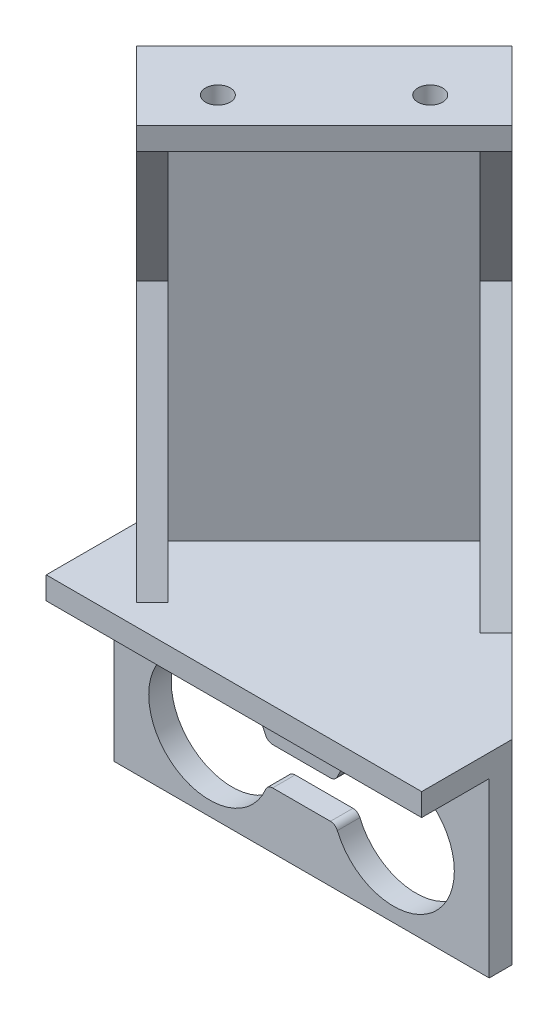
SolidWorks part; units mm, degrees
other "标注1"
sketch "草图6" plane through (25, -10, 15) normal (0.0929, -0.9273, 0.3626) x (0.5024, 0.3581, 0.787)
other "标注2"
sketch "草图7" plane through (25, -10, 15) normal (0.0929, -0.9273, 0.3626) x (0.5024, 0.3581, 0.787)
other "标注3"
sketch "草图8" plane through (25, -10, 15) normal (0.0929, -0.9273, 0.3626) x (0.5024, 0.3581, 0.787)
ref_plane "前视基准面" through (0, 0, 0) normal (0, 0, 1) x (1, 0, 0)
ref_plane "上视基准面" through (0, 0, 0) normal (0, 1, 0) x (1, 0, 0)
ref_plane "右视基准面" through (0, 0, 0) normal (1, 0, 0) x (0, 0, -1)
sketch "草图1" plane through (0, 0, 0) normal (0, 0, 1) x (1, 0, 0)
  line L1 (25, -10) -> (-25, -10)
  line L2 (25, -10) -> (25, 10)
  line L3 (25, 10) -> (-25, 10)
  line L4 (-25, -10) -> (-25, 10)
  line L5 (25, -10) -> (-25, 10) construction
  line L6 (25, 10) -> (-25, -10) construction
  line L8 (-3.85, 2.5) -> (3.85, 2.5)
  line L9 (3.85, -2.5) -> (-3.85, -2.5)
  line L10 (3.25, 7.25) -> (-3.25, 7.25) construction
  line L11 (3.25, 5.5) -> (-3.25, 5.5)
  line L12 (3.25, 9) -> (-3.25, 9)
  arc A7 (4.7731, -3.1154) -> (4.7731, 3.1154) centre (12.25, 0) ccw
  arc A8 (-4.7731, 3.1154) -> (-4.7731, -3.1154) centre (-12.25, 0) ccw
  arc A9 (3.85, -2.5) -> (4.7731, -3.1154) centre (3.85, -3.5) cw
  arc A10 (3.85, 2.5) -> (4.7731, 3.1154) centre (3.85, 3.5) ccw
  arc A11 (-3.85, -2.5) -> (-4.7731, -3.1154) centre (-3.85, -3.5) ccw
  arc A12 (-3.85, 2.5) -> (-4.7731, 3.1154) centre (-3.85, 3.5) cw
  arc A13 (3.25, 5.5) -> (3.25, 9) centre (3.25, 7.25) ccw
  arc A14 (-3.25, 9) -> (-3.25, 5.5) centre (-3.25, 7.25) ccw
  point P0 (0, 0)
  point P22 (0, 7.25)
  dimension "D3" = 1
  dimension "D4" = 8.1
  dimension "D5" = 8.1
  dimension "D6" = 2.5
  dimension "D8" = 12.25
  dimension "D9" = 12.25
  dimension "D12" = 1.75
  dimension "D1" = 20
  dimension "D2" = 50
  dimension "D7" = 2.5
  dimension "D10" = 7.25
  dimension "D11" = 6.5
  dimension "D13" = 3.25
extrude "凸台-拉伸1" add sketch "草图1" along normal blind 3
sketch "草图2" plane through (0, 10, 0) normal (0, 1, 0) x (1, 0, 0)
  line L1 (-25, 0) -> (25, 0)
  line L2 (-25, 0) -> (-25, -12)
  line L3 (-25, -12) -> (25, -12)
  line L4 (25, 0) -> (25, -12)
  dimension "D1" = 12
extrude "凸台-拉伸2" add sketch "草图2" along normal blind 6
sketch "草图5" plane through (0, 10, 0) normal (0, -1, 0) x (1, 0, 0)
  line L1 (25, 3) -> (-25, 3)
  line L2 (25, 3) -> (25, 12)
  line L3 (25, 12) -> (-25, 12)
  line L4 (-25, 3) -> (-25, 12)
extrude "切除-拉伸2" cut sketch "草图5" against normal blind 3
sketch "草图9" plane through (0, 16, 0) normal (0, 1, 0) x (1, 0, 0)
  line L0 (25, 0) -> (0, 25)
  line L1 (0, 25) -> (-25, 0)
  line L2 (25, 0) -> (-25, 0)
extrude "凸台-拉伸3" add sketch "草图9" against normal blind 3
sketch "草图11" plane through (0, 16, 0) normal (0, 1, 0) x (1, 0, 0)
  line L0 (0, 25) -> (2.1213, 22.8787)
  line L1 (25, 0) -> (0, 25) construction
  line L2 (2.1213, 22.8787) -> (-22.8787, -2.1213)
  line L3 (-25, 0) -> (-22.8787, -2.1213)
  line L9 (-25, 0) -> (-25, -12)
  line L10 (-25, -12) -> (25, -12)
  line L11 (25, -12) -> (25, 0)
  line L12 (25, 0) -> (0, 25)
  line L13 (0, 25) -> (-25, 0)
  line L18 (0, 25) -> (-25, 0)
  dimension "D1" = 0
extrude "凸台-拉伸4" add sketch "草图11" along normal blind 55 contours L18 L3 L2 L0
sketch "草图12" plane through (-10.3787, 0, -10.3787) normal (0.7071, 0, 0.7071) x (0.7071, 0, -0.7071)
  line L2 (-17.6777, 71) -> (-17.6777, 68)
  line L5 (14.6777, 68) -> (-17.6777, 68)
  line L6 (14.6777, 68) -> (14.6777, 71)
  line L7 (14.6777, 71) -> (-17.6777, 71)
extrude "凸台-拉伸6" add sketch "草图12" along normal blind 10
sketch "草图13" plane through (12.5, 0, -12.5) normal (0.7071, 0, -0.7071) x (-0.7071, 0, -0.7071)
  line L0 (17.6777, 71) -> (4.6777, 71)
  line L1 (17.6777, 71) -> (17.6777, 46)
  line L2 (17.6777, 13) -> (17.6777, 71) construction
  line L3 (4.6777, 71) -> (4.6777, 68)
  line L4 (17.6777, 46) -> (14.6777, 46)
  line L5 (14.6777, 71) -> (14.6777, 16) construction
  line L6 (14.6777, 46) -> (4.6777, 68)
  line L7 (14.6777, 16) -> (-0.3223, 16)
  line L8 (-17.6777, 16) -> (14.6777, 16) construction
  line L9 (14.6777, 16) -> (14.6777, 46)
  line L10 (14.6777, 46) -> (-0.3223, 16)
  line L11 (4.6777, 68) -> (4.6777, 71) construction
  line M6 (14.6777, 16) -> (-17.6777, 16)
  line M11 (14.6777, 71) -> (14.6777, 16)
  dimension "D1" = 15
  dimension "D2" = 30
  dimension "D3" = 13
extrude "凸台-拉伸7" add sketch "草图13" against normal blind 3 contours L10 M11 M6 | L6 L0 L3 M11
sketch "草图14" plane through (-12.5, 0, 12.5) normal (-0.7071, 0, 0.7071) x (0.7071, 0, 0.7071)
  line L0 (-14.6777, 16) -> (-4.6777, 16)
  line L1 (-14.6777, 16) -> (-14.6777, 46)
  line L2 (-14.6777, 68) -> (-14.6777, 16) construction
  line L3 (-4.6777, 16) -> (-14.6777, 46)
  line L4 (-14.6777, 46) -> (-4.6777, 68)
  line L5 (-4.6777, 68) -> (-14.6777, 68)
  line L6 (-14.6777, 68) -> (-14.6777, 46)
  line M2 (-14.6777, 16) -> (-14.6777, 68)
  line M3 (-14.6777, 68) -> (-4.6777, 68)
  dimension "D1" = 30
  dimension "D2" = 10
extrude "凸台-拉伸8" add sketch "草图14" against normal blind 3 contours L0 L3 M2 | L4 M2 M3
sketch "草图15" plane through (0, 68, 0) normal (0, -1, 0) x (1, 0, 0)
  line L0 (7.0711, -13.6863) -> (0, -20.7574) construction
  line L1 (3.5355, -17.2218) -> (0.2279, -13.9142)
  line L2 (-20.7574, 0) -> (-13.6863, 7.0711) construction
  line L3 (-17.2218, 3.5355) -> (-13.9142, 0.2279)
  line L4 (0, -25) -> (-25, 0) construction
  circle A0 centre (0.2279, -13.9142) radius 1.65
  circle A1 centre (-13.9142, 0.2279) radius 1.65
  dimension "D1" = 20
extrude "切除-拉伸3" cut sketch "草图15" against normal blind 3
move or copy body "实体-移动/复制1" [suppressed] bodies to move or copy 118
